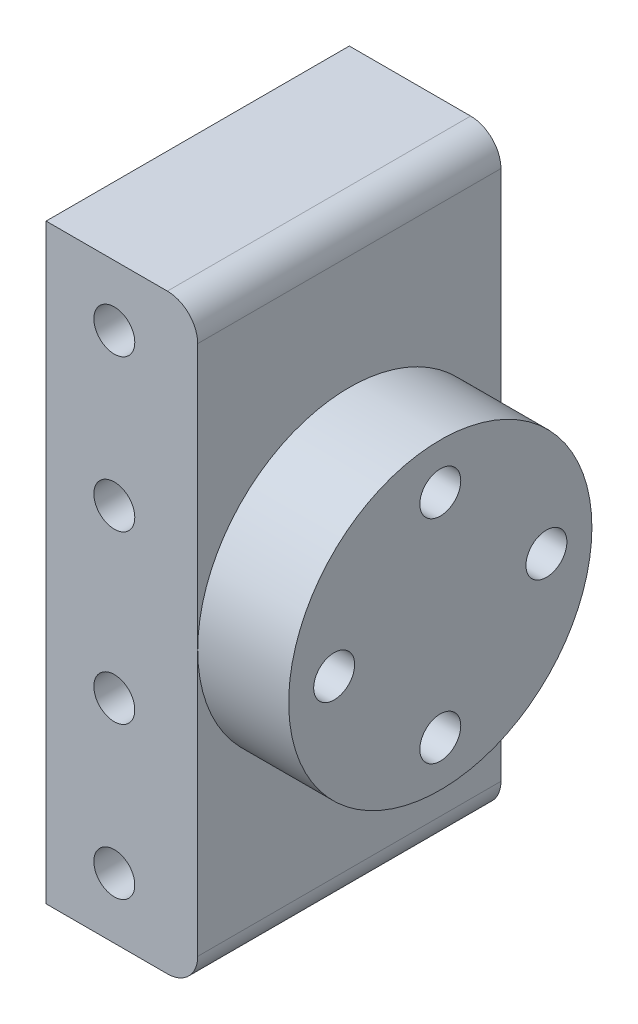
SolidWorks part; units mm, degrees
ref_plane "Front Plane" through (0, 0, 0) normal (0, 0, 1) x (1, 0, 0)
ref_plane "Top Plane" through (0, 0, 0) normal (0, 1, 0) x (1, 0, 0)
ref_plane "Right Plane" through (0, 0, 0) normal (1, 0, 0) x (0, 0, -1)
sketch "Sketch1" plane through (0, 0, 0) normal (0, 0, 1) x (1, 0, 0)
  line L1 (-5, -19.5) -> (3, -19.5)
  line L2 (-5, -19.5) -> (-5, 19.5)
  line L3 (-5, 19.5) -> (3, 19.5)
  line L4 (5, -17.5) -> (5, 17.5)
  line L5 (-5, -19.5) -> (5, 19.5) construction
  line L6 (-5, 19.5) -> (5, -19.5) construction
  arc A0 (3, -19.5) -> (5, -17.5) centre (3, -17.5) ccw
  arc A1 (3, 19.5) -> (5, 17.5) centre (3, 17.5) cw
  point P0 (0, 0)
  dimension "D3" = 2
  dimension "D1" = 39
  dimension "D2" = 10
extrude "Boss-Extrude1" add sketch "Sketch1" along normal blind 20
sketch "Sketch2" plane through (0, 0, 20) normal (0, 0, 1) x (1, 0, 0)
  line L3 (-5, 19.5) -> (-5, -19.5) construction
  line L4 (-5, 0) -> (5, 0) construction
  line L5 (5, -17.5) -> (5, 17.5) construction
  line L6 (-0.5, 5.5) -> (-0.5, -5.5) construction
  circle A0 centre (-0.5, 15.5) radius 1.35
  circle A4 centre (-0.5, 5.5) radius 1.35
  circle A5 centre (-0.5, -15.5) radius 1.35
  circle A6 centre (-0.5, -5.5) radius 1.35
  dimension "D1" = 11
  dimension "D2" = 4.5
  dimension "D3" = 2.7
  dimension "D5" = 10
  dimension "D4" = 2
extrude "Cut-Extrude2" cut sketch "Sketch2" against normal blind 12
sketch "Sketch3" plane through (5, 0, 0) normal (1, 0, 0) x (0, 0, -1)
  line L0 (-20, -17.5) -> (0, 17.5) construction
  circle A0 centre (-10, 0) radius 10
  point P6 (-10, 0)
  dimension "D1" = 20
extrude "Boss-Extrude2" add sketch "Sketch3" along normal blind 6
sketch "Sketch4" plane through (11, 0, 0) normal (1, 0, 0) x (0, 0, -1)
  line L0 (-20, -17.5) -> (0, 17.5) construction
  line L2 (-10, -7) -> (-3, 0) construction
  line L3 (-10, -7) -> (-17, 0) construction
  line L4 (-17, 0) -> (-10, 7) construction
  line L5 (-3, 0) -> (-10, 7) construction
  line L6 (-10, -7) -> (-10, 7) construction
  line L7 (-17, 0) -> (-3, 0) construction
  circle A0 centre (-17, 0) radius 1.35
  circle A1 centre (-10, 7) radius 1.35
  circle A2 centre (-3, 0) radius 1.35
  circle A3 centre (-10, -7) radius 1.35
  point P4 (-10, 0)
  point P13 (-5.0473, -4.9467)
  point P14 (-3, 0)
  point P15 (0, 0)
  dimension "D2" = 2.7
  dimension "D1" = 7
extrude "Cut-Extrude3" cut sketch "Sketch4" against normal blind 10
